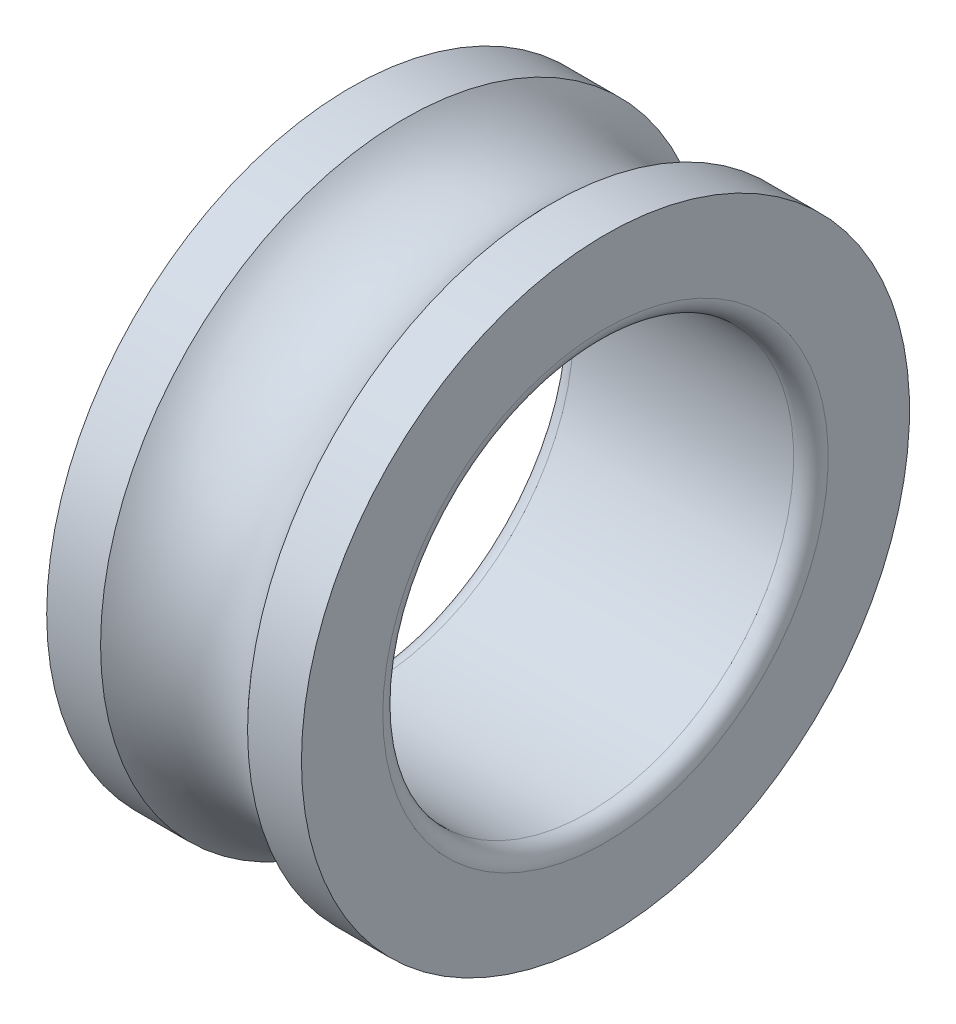
SolidWorks part; units mm, degrees
ref_plane "Front Plane" through (0, 0, 0) normal (0, 0, 1) x (1, 0, 0)
ref_plane "Top Plane" through (0, 0, 0) normal (0, 1, 0) x (1, 0, 0)
ref_plane "Right Plane" through (0, 0, 0) normal (1, 0, 0) x (0, 0, -1)
sketch "Sketch1" plane through (0, 0, 0) normal (0, 0, 1) x (1, 0, 0)
  line L0 (-15.5, 0) -> (65.1655, 0) construction
  line L1 (0, 25) -> (0, 0) construction
  line L2 (13.4, 25) -> (-13.4, 25)
  line L3 (15.5, 27.1) -> (15.5, 37)
  line L4 (15.5, 37) -> (8.9443, 37)
  line L5 (-15.5, 27.1) -> (-15.5, 37)
  line L6 (15.5, 25) -> (-15.5, 37) construction
  line L7 (15.5, 37) -> (-15.5, 25) construction
  line L8 (-8.9443, 37) -> (-15.5, 37)
  arc A0 (-8.9443, 37) -> (8.9443, 37) centre (0, 45) ccw
  arc A1 (13.4, 25) -> (15.5, 27.1) centre (13.4, 27.1) ccw
  arc A2 (-13.4, 25) -> (-15.5, 27.1) centre (-13.4, 27.1) cw
  point P3 (0, 31)
  dimension "D5" = 12
  dimension "D6" = 2.1
  dimension "D1" = 31
  dimension "D2" = 25
  dimension "D3" = 37
  dimension "D4" = 8
revolve "Revolve1" add sketch "Sketch1" angle 360 about L0
